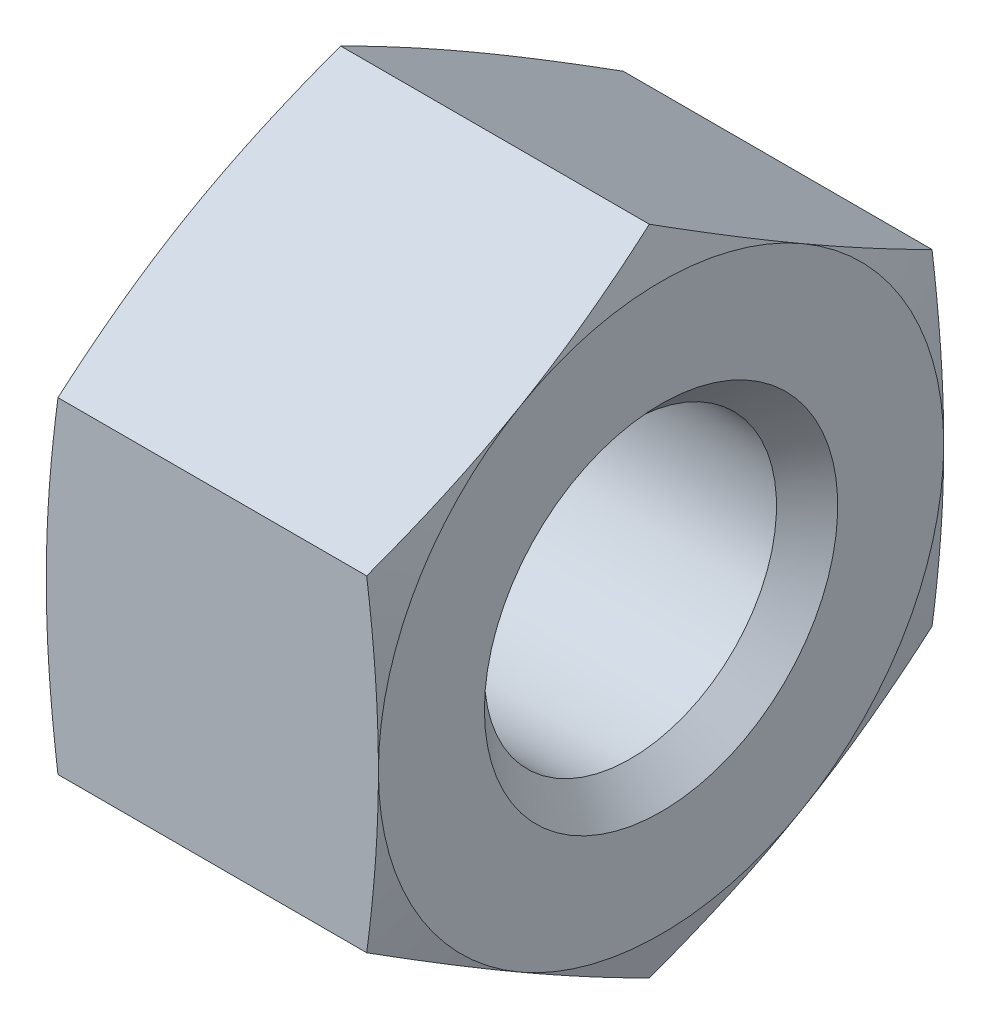
SolidWorks part; units mm, degrees
ref_plane "Front Plane" through (0, 0, 0) normal (0, 0, 1) x (1, 0, 0)
ref_plane "Top Plane" through (0, 0, 0) normal (0, 1, 0) x (1, 0, 0)
ref_plane "Right Plane" through (0, 0, 0) normal (1, 0, 0) x (0, 0, -1)
ref_plane "Plane1" through (0, 0, 0) normal (0, 0, 1) x (1, 0, 0)
sketch "Sketch1" plane through (0, 0, 0) normal (0, 0, 1) x (1, 0, 0)
  line L0 (-2.35, 0) -> (-2.35, 4)
  line L1 (-2.35, 4) -> (-2.1356, 4.8)
  line L2 (-2.1356, 4.8) -> (2.1356, 4.8)
  line L3 (2.1356, 4.8) -> (2.35, 4)
  line L4 (2.35, 4) -> (2.35, 0)
  line L5 (2.35, 0) -> (-2.35, 0)
  line L6 (2.35, 0) -> (-2.35, 0) construction
revolve "Revolve1" add sketch "Sketch1" angle 360 about L6
ref_plane "Plane2" through (0, 0, 0) normal (0, 0, 1) x (1, 0, 0)
sketch "Sketch2" plane through (0, 0, 0) normal (0, 0, 1) x (1, 0, 0)
  line L0 (-2.35, 0) -> (-2.35, 2.5)
  line L1 (-2.35, 2.5) -> (-1.917, 2.067)
  line L2 (-1.917, 2.067) -> (1.917, 2.067)
  line L3 (1.917, 2.067) -> (2.35, 2.5)
  line L4 (2.35, 2.5) -> (2.35, 0)
  line L5 (2.35, 0) -> (-2.35, 0)
  line L6 (2.35, 0) -> (-2.35, 0) construction
revolve "Cut-Revolve1" cut sketch "Sketch2" angle 360 about L6
ref_plane "Plane3" through (0, 0, 0) normal (1, 0, 0) x (0, 0, -1)
sketch "Sketch3" plane through (0, 0, 0) normal (1, 0, 0) x (0, 0, -1)
  line L0 (-8, -8) -> (8, -8)
  line L1 (8, -8) -> (8, 8)
  line L2 (8, 8) -> (-8, 8)
  line L3 (-8, 8) -> (-8, -8)
  line L4 (-4, 2.3094) -> (-4, -2.3094)
  line L5 (-4, -2.3094) -> (0, -4.6188)
  line L6 (0, -4.6188) -> (4, -2.3094)
  line L7 (4, -2.3094) -> (4, 2.3094)
  line L8 (4, 2.3094) -> (0, 4.6188)
  line L9 (0, 4.6188) -> (-4, 2.3094)
extrude "Cut-Extrude1" cut sketch "Sketch3" against normal blind 4.7 and the other way blind 4.7
